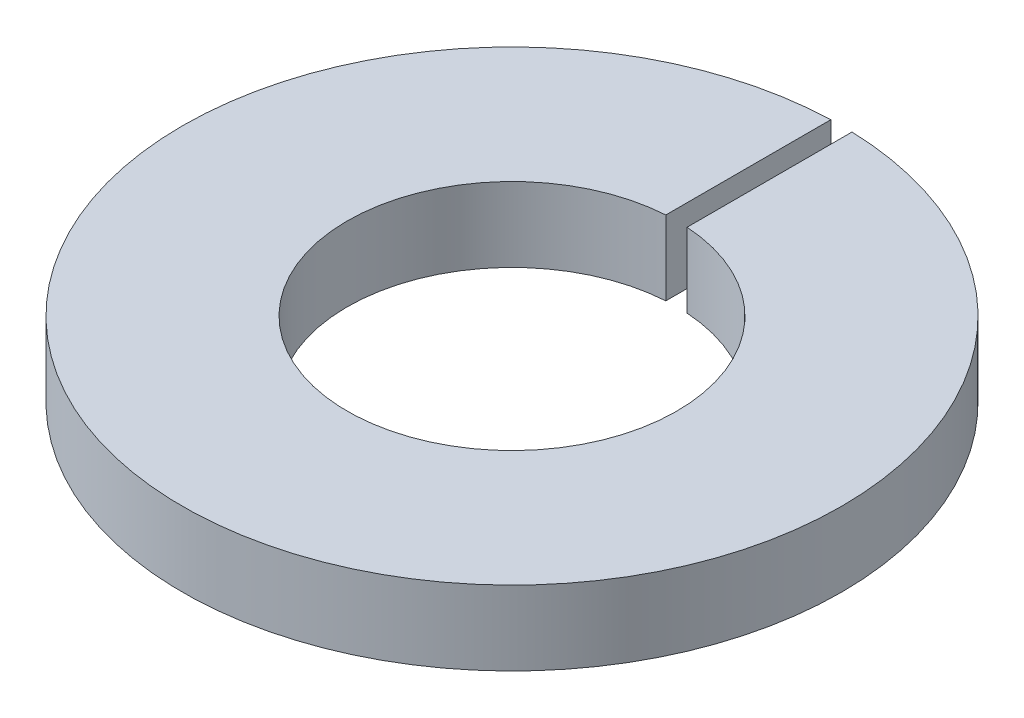
SolidWorks part; units mm, degrees
material "1.4057 (X17CrNi16-2)"
ref_plane "Plano frontal" through (0, 0, 0) normal (0, 0, 1) x (1, 0, 0)
ref_plane "Plano superior" through (0, 0, 0) normal (0, 1, 0) x (1, 0, 0)
ref_plane "Plano direito" through (0, 0, 0) normal (1, 0, 0) x (0, 0, -1)
sketch "Esboço1" plane through (0, 0, 0) normal (0, 1, 0) x (1, 0, 0)
  line L0 (-0.1, 3.0984) -> (-0.1, 1.5468)
  line L1 (0.1, 3.0984) -> (0.1, 1.5468)
  line L2 (0, 0) -> (0, 4.1585) construction
  line L3 (0.1, 2.3226) -> (0, 2.3226) construction
  line L4 (0, 2.3226) -> (-0.1, 2.3226) construction
  arc A2 (-0.1, 1.5468) -> (0.1, 1.5468) centre (0, 0) ccw
  arc A3 (-0.1, 3.0984) -> (0.1, 3.0984) centre (0, 0) ccw
  dimension "D1" = 1.55
  dimension "D2" = 3.1
  dimension "D3" = 0.2
extrude "Ressalto-extrusão1" add sketch "Esboço1" along normal blind 0.7
